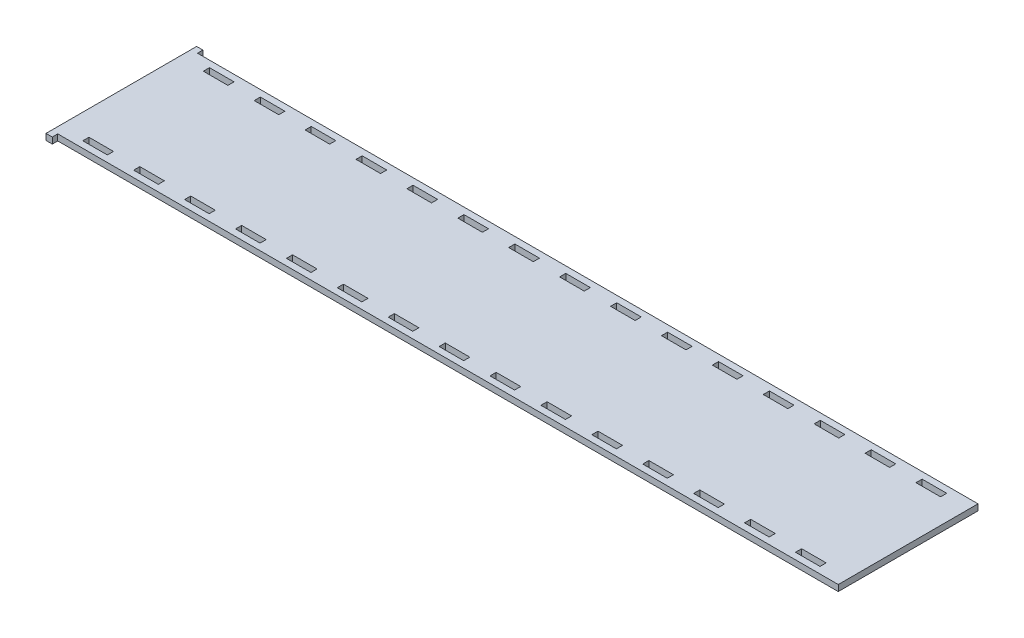
SolidWorks part; units mm, degrees
ref_plane "Front" through (0, 0, 0) normal (0, 0, 1) x (1, 0, 0)
ref_plane "Top" through (0, 0, 0) normal (0, 1, 0) x (1, 0, 0)
ref_plane "Right" through (0, 0, 0) normal (1, 0, 0) x (0, 0, -1)
sketch "Sketch1" plane through (0, 0, 0) normal (0, 1, 0) x (1, 0, 0)
  line L0 (-164.2929, -32.8311) -> (-151.3929, -32.8311) construction
  line L1 (-164.2929, -29.4529) -> (-164.2929, -32.8311) construction
  line L2 (-151.3929, -29.4529) -> (-164.2929, -29.4529) construction
  line L3 (-151.3929, -32.8311) -> (-151.3929, -29.4529) construction
  line L4 (177.7, -32.8311) -> (190.6, -32.8311) construction
  line L5 (177.7, -29.4529) -> (177.7, -32.8311) construction
  line L6 (190.6, -29.4529) -> (177.7, -29.4529) construction
  line L7 (190.6, -32.8311) -> (190.6, -29.4529) construction
  line L8 (-137.9857, -32.8311) -> (-125.0857, -32.8311) construction
  line L9 (-137.9857, -29.4529) -> (-137.9857, -32.8311) construction
  line L10 (-125.0857, -29.4529) -> (-137.9857, -29.4529) construction
  line L11 (-125.0857, -32.8311) -> (-125.0857, -29.4529) construction
  line L12 (-111.6786, -32.8311) -> (-98.7786, -32.8311) construction
  line L13 (-111.6786, -29.4529) -> (-111.6786, -32.8311) construction
  line L14 (-98.7786, -29.4529) -> (-111.6786, -29.4529) construction
  line L15 (-98.7786, -32.8311) -> (-98.7786, -29.4529) construction
  line L16 (151.3929, -32.8311) -> (164.2929, -32.8311) construction
  line L17 (151.3929, -29.4529) -> (151.3929, -32.8311) construction
  line L18 (164.2929, -29.4529) -> (151.3929, -29.4529) construction
  line L19 (164.2929, -32.8311) -> (164.2929, -29.4529) construction
  line L20 (125.0857, -32.8311) -> (137.9857, -32.8311) construction
  line L21 (125.0857, -29.4529) -> (125.0857, -32.8311) construction
  line L22 (137.9857, -29.4529) -> (125.0857, -29.4529) construction
  line L23 (137.9857, -32.8311) -> (137.9857, -29.4529) construction
  line L24 (98.7786, -32.8311) -> (111.6786, -32.8311) construction
  line L25 (98.7786, -29.4529) -> (98.7786, -32.8311) construction
  line L26 (111.6786, -29.4529) -> (98.7786, -29.4529) construction
  line L27 (111.6786, -32.8311) -> (111.6786, -29.4529) construction
  line L28 (72.4714, -32.8311) -> (85.3714, -32.8311) construction
  line L29 (72.4714, -29.4529) -> (72.4714, -32.8311) construction
  line L30 (85.3714, -29.4529) -> (72.4714, -29.4529) construction
  line L31 (85.3714, -32.8311) -> (85.3714, -29.4529) construction
  line L32 (46.1643, -32.8311) -> (59.0643, -32.8311) construction
  line L33 (46.1643, -29.4529) -> (46.1643, -32.8311) construction
  line L34 (59.0643, -29.4529) -> (46.1643, -29.4529) construction
  line L35 (59.0643, -32.8311) -> (59.0643, -29.4529) construction
  line L36 (19.8571, -32.8311) -> (32.7571, -32.8311) construction
  line L37 (19.8571, -29.4529) -> (19.8571, -32.8311) construction
  line L38 (32.7571, -29.4529) -> (19.8571, -29.4529) construction
  line L39 (32.7571, -32.8311) -> (32.7571, -29.4529) construction
  line L40 (-6.45, -32.8311) -> (6.45, -32.8311) construction
  line L41 (-6.45, -29.4529) -> (-6.45, -32.8311) construction
  line L42 (6.45, -29.4529) -> (-6.45, -29.4529) construction
  line L43 (6.45, -32.8311) -> (6.45, -29.4529) construction
  line L44 (-32.7571, -32.8311) -> (-19.8571, -32.8311) construction
  line L45 (-32.7571, -29.4529) -> (-32.7571, -32.8311) construction
  line L46 (-19.8571, -29.4529) -> (-32.7571, -29.4529) construction
  line L47 (-19.8571, -32.8311) -> (-19.8571, -29.4529) construction
  line L48 (-59.0643, -32.8311) -> (-46.1643, -32.8311) construction
  line L49 (-59.0643, -29.4529) -> (-59.0643, -32.8311) construction
  line L50 (-46.1643, -29.4529) -> (-59.0643, -29.4529) construction
  line L51 (-46.1643, -32.8311) -> (-46.1643, -29.4529) construction
  line L52 (-85.3714, -32.8311) -> (-72.4714, -32.8311) construction
  line L53 (-85.3714, -29.4529) -> (-85.3714, -32.8311) construction
  line L54 (-72.4714, -29.4529) -> (-85.3714, -29.4529) construction
  line L55 (-72.4714, -32.8311) -> (-72.4714, -29.4529) construction
  line L56 (-190.6, -32.8311) -> (-177.7, -32.8311) construction
  line L57 (-190.6, -29.4529) -> (-190.6, -32.8311) construction
  line L58 (-177.7, -29.4529) -> (-190.6, -29.4529) construction
  line L59 (-177.7, -32.8311) -> (-177.7, -29.4529) construction
  line L60 (190.6, 32.8311) -> (177.7, 32.8311) construction
  line L61 (190.6, 29.4529) -> (190.6, 32.8311) construction
  line L62 (177.7, 29.4529) -> (190.6, 29.4529) construction
  line L63 (177.7, 32.8311) -> (177.7, 29.4529) construction
  line L64 (-151.3929, 32.8311) -> (-164.2929, 32.8311) construction
  line L65 (-151.3929, 29.4529) -> (-151.3929, 32.8311) construction
  line L66 (-164.2929, 29.4529) -> (-151.3929, 29.4529) construction
  line L67 (-164.2929, 32.8311) -> (-164.2929, 29.4529) construction
  line L68 (-125.0857, 32.8311) -> (-137.9857, 32.8311) construction
  line L69 (-125.0857, 29.4529) -> (-125.0857, 32.8311) construction
  line L70 (-137.9857, 29.4529) -> (-125.0857, 29.4529) construction
  line L71 (-137.9857, 32.8311) -> (-137.9857, 29.4529) construction
  line L72 (-98.7786, 32.8311) -> (-111.6786, 32.8311) construction
  line L73 (-98.7786, 29.4529) -> (-98.7786, 32.8311) construction
  line L74 (-111.6786, 29.4529) -> (-98.7786, 29.4529) construction
  line L75 (-111.6786, 32.8311) -> (-111.6786, 29.4529) construction
  line L76 (-72.4714, 32.8311) -> (-85.3714, 32.8311) construction
  line L77 (-72.4714, 29.4529) -> (-72.4714, 32.8311) construction
  line L78 (-85.3714, 29.4529) -> (-72.4714, 29.4529) construction
  line L79 (-85.3714, 32.8311) -> (-85.3714, 29.4529) construction
  line L80 (-46.1643, 32.8311) -> (-59.0643, 32.8311) construction
  line L81 (-46.1643, 29.4529) -> (-46.1643, 32.8311) construction
  line L82 (-59.0643, 29.4529) -> (-46.1643, 29.4529) construction
  line L83 (-59.0643, 32.8311) -> (-59.0643, 29.4529) construction
  line L84 (-19.8571, 32.8311) -> (-32.7571, 32.8311) construction
  line L85 (-19.8571, 29.4529) -> (-19.8571, 32.8311) construction
  line L86 (-32.7571, 29.4529) -> (-19.8571, 29.4529) construction
  line L87 (-32.7571, 32.8311) -> (-32.7571, 29.4529) construction
  line L88 (6.45, 32.8311) -> (-6.45, 32.8311) construction
  line L89 (6.45, 29.4529) -> (6.45, 32.8311) construction
  line L90 (-6.45, 29.4529) -> (6.45, 29.4529) construction
  line L91 (-6.45, 32.8311) -> (-6.45, 29.4529) construction
  line L92 (32.7571, 32.8311) -> (19.8571, 32.8311) construction
  line L93 (32.7571, 29.4529) -> (32.7571, 32.8311) construction
  line L94 (19.8571, 29.4529) -> (32.7571, 29.4529) construction
  line L95 (19.8571, 32.8311) -> (19.8571, 29.4529) construction
  line L96 (59.0643, 32.8311) -> (46.1643, 32.8311) construction
  line L97 (59.0643, 29.4529) -> (59.0643, 32.8311) construction
  line L98 (46.1643, 29.4529) -> (59.0643, 29.4529) construction
  line L99 (46.1643, 32.8311) -> (46.1643, 29.4529) construction
  line L100 (85.3714, 32.8311) -> (72.4714, 32.8311) construction
  line L101 (85.3714, 29.4529) -> (85.3714, 32.8311) construction
  line L102 (72.4714, 29.4529) -> (85.3714, 29.4529) construction
  line L103 (72.4714, 32.8311) -> (72.4714, 29.4529) construction
  line L104 (111.6786, 32.8311) -> (98.7786, 32.8311) construction
  line L105 (111.6786, 29.4529) -> (111.6786, 32.8311) construction
  line L106 (98.7786, 29.4529) -> (111.6786, 29.4529) construction
  line L107 (98.7786, 32.8311) -> (98.7786, 29.4529) construction
  line L108 (137.9857, 32.8311) -> (125.0857, 32.8311) construction
  line L109 (137.9857, 29.4529) -> (137.9857, 32.8311) construction
  line L110 (125.0857, 29.4529) -> (137.9857, 29.4529) construction
  line L111 (125.0857, 32.8311) -> (125.0857, 29.4529) construction
  line L112 (164.2929, 32.8311) -> (151.3929, 32.8311) construction
  line L113 (164.2929, 29.4529) -> (164.2929, 32.8311) construction
  line L114 (151.3929, 29.4529) -> (164.2929, 29.4529) construction
  line L115 (151.3929, 32.8311) -> (151.3929, 29.4529) construction
  line L116 (-177.7, 32.8311) -> (-190.6, 32.8311) construction
  line L117 (-177.7, 29.4529) -> (-177.7, 32.8311) construction
  line L118 (-190.6, 29.4529) -> (-177.7, 29.4529) construction
  line L119 (-190.6, 32.8311) -> (-190.6, 29.4529) construction
  line L120 (-200.1504, 36.0061) -> (-200.1504, 38.8239) construction
  line L121 (-200.1504, 38.8239) -> (-203.2, 38.8239) construction
  line L122 (-203.2, 38.8239) -> (-203.2, -38.8239) construction
  line L123 (-203.2, -38.8239) -> (-200.1504, -38.8239) construction
  line L124 (-200.1504, -38.8239) -> (-200.1504, -36.0061) construction
  line L125 (-200.1504, -36.0061) -> (203.2, -36.0061) construction
  line L126 (203.2, -36.0061) -> (203.2, 36.0061) construction
  line L127 (203.2, 36.0061) -> (-200.1504, 36.0061) construction
  line L128 (-164.1913, -32.7295) -> (-151.4945, -32.7295)
  line L129 (-151.4945, -32.7295) -> (-151.4945, -29.5545)
  line L130 (-151.4945, -29.5545) -> (-164.1913, -29.5545)
  line L131 (-164.1913, -29.5545) -> (-164.1913, -32.7295)
  line L132 (177.8016, -32.7295) -> (190.4984, -32.7295)
  line L133 (190.4984, -32.7295) -> (190.4984, -29.5545)
  line L134 (190.4984, -29.5545) -> (177.8016, -29.5545)
  line L135 (177.8016, -29.5545) -> (177.8016, -32.7295)
  line L136 (-137.8841, -32.7295) -> (-125.1873, -32.7295)
  line L137 (-125.1873, -32.7295) -> (-125.1873, -29.5545)
  line L138 (-125.1873, -29.5545) -> (-137.8841, -29.5545)
  line L139 (-137.8841, -29.5545) -> (-137.8841, -32.7295)
  line L140 (-111.577, -32.7295) -> (-98.8802, -32.7295)
  line L141 (-98.8802, -32.7295) -> (-98.8802, -29.5545)
  line L142 (-98.8802, -29.5545) -> (-111.577, -29.5545)
  line L143 (-111.577, -29.5545) -> (-111.577, -32.7295)
  line L144 (151.4945, -32.7295) -> (164.1913, -32.7295)
  line L145 (164.1913, -32.7295) -> (164.1913, -29.5545)
  line L146 (164.1913, -29.5545) -> (151.4945, -29.5545)
  line L147 (151.4945, -29.5545) -> (151.4945, -32.7295)
  line L148 (125.1873, -32.7295) -> (137.8841, -32.7295)
  line L149 (137.8841, -32.7295) -> (137.8841, -29.5545)
  line L150 (137.8841, -29.5545) -> (125.1873, -29.5545)
  line L151 (125.1873, -29.5545) -> (125.1873, -32.7295)
  line L152 (98.8802, -32.7295) -> (111.577, -32.7295)
  line L153 (111.577, -32.7295) -> (111.577, -29.5545)
  line L154 (111.577, -29.5545) -> (98.8802, -29.5545)
  line L155 (98.8802, -29.5545) -> (98.8802, -32.7295)
  line L156 (72.573, -32.7295) -> (85.2698, -32.7295)
  line L157 (85.2698, -32.7295) -> (85.2698, -29.5545)
  line L158 (85.2698, -29.5545) -> (72.573, -29.5545)
  line L159 (72.573, -29.5545) -> (72.573, -32.7295)
  line L160 (46.2659, -32.7295) -> (58.9627, -32.7295)
  line L161 (58.9627, -32.7295) -> (58.9627, -29.5545)
  line L162 (58.9627, -29.5545) -> (46.2659, -29.5545)
  line L163 (46.2659, -29.5545) -> (46.2659, -32.7295)
  line L164 (19.9587, -32.7295) -> (32.6555, -32.7295)
  line L165 (32.6555, -32.7295) -> (32.6555, -29.5545)
  line L166 (32.6555, -29.5545) -> (19.9587, -29.5545)
  line L167 (19.9587, -29.5545) -> (19.9587, -32.7295)
  line L168 (-6.3484, -32.7295) -> (6.3484, -32.7295)
  line L169 (6.3484, -32.7295) -> (6.3484, -29.5545)
  line L170 (6.3484, -29.5545) -> (-6.3484, -29.5545)
  line L171 (-6.3484, -29.5545) -> (-6.3484, -32.7295)
  line L172 (-32.6555, -32.7295) -> (-19.9587, -32.7295)
  line L173 (-19.9587, -32.7295) -> (-19.9587, -29.5545)
  line L174 (-19.9587, -29.5545) -> (-32.6555, -29.5545)
  line L175 (-32.6555, -29.5545) -> (-32.6555, -32.7295)
  line L176 (-58.9627, -32.7295) -> (-46.2659, -32.7295)
  line L177 (-46.2659, -32.7295) -> (-46.2659, -29.5545)
  line L178 (-46.2659, -29.5545) -> (-58.9627, -29.5545)
  line L179 (-58.9627, -29.5545) -> (-58.9627, -32.7295)
  line L180 (-85.2698, -32.7295) -> (-72.573, -32.7295)
  line L181 (-72.573, -32.7295) -> (-72.573, -29.5545)
  line L182 (-72.573, -29.5545) -> (-85.2698, -29.5545)
  line L183 (-85.2698, -29.5545) -> (-85.2698, -32.7295)
  line L184 (-190.4984, -32.7295) -> (-177.8016, -32.7295)
  line L185 (-177.8016, -32.7295) -> (-177.8016, -29.5545)
  line L186 (-177.8016, -29.5545) -> (-190.4984, -29.5545)
  line L187 (-190.4984, -29.5545) -> (-190.4984, -32.7295)
  line L188 (190.4984, 32.7295) -> (177.8016, 32.7295)
  line L189 (177.8016, 32.7295) -> (177.8016, 29.5545)
  line L190 (177.8016, 29.5545) -> (190.4984, 29.5545)
  line L191 (190.4984, 29.5545) -> (190.4984, 32.7295)
  line L192 (-151.4945, 32.7295) -> (-164.1913, 32.7295)
  line L193 (-164.1913, 32.7295) -> (-164.1913, 29.5545)
  line L194 (-164.1913, 29.5545) -> (-151.4945, 29.5545)
  line L195 (-151.4945, 29.5545) -> (-151.4945, 32.7295)
  line L196 (-125.1873, 32.7295) -> (-137.8841, 32.7295)
  line L197 (-137.8841, 32.7295) -> (-137.8841, 29.5545)
  line L198 (-137.8841, 29.5545) -> (-125.1873, 29.5545)
  line L199 (-125.1873, 29.5545) -> (-125.1873, 32.7295)
  line L200 (-98.8802, 32.7295) -> (-111.577, 32.7295)
  line L201 (-111.577, 32.7295) -> (-111.577, 29.5545)
  line L202 (-111.577, 29.5545) -> (-98.8802, 29.5545)
  line L203 (-98.8802, 29.5545) -> (-98.8802, 32.7295)
  line L204 (-72.573, 32.7295) -> (-85.2698, 32.7295)
  line L205 (-85.2698, 32.7295) -> (-85.2698, 29.5545)
  line L206 (-85.2698, 29.5545) -> (-72.573, 29.5545)
  line L207 (-72.573, 29.5545) -> (-72.573, 32.7295)
  line L208 (-46.2659, 32.7295) -> (-58.9627, 32.7295)
  line L209 (-58.9627, 32.7295) -> (-58.9627, 29.5545)
  line L210 (-58.9627, 29.5545) -> (-46.2659, 29.5545)
  line L211 (-46.2659, 29.5545) -> (-46.2659, 32.7295)
  line L212 (-19.9587, 32.7295) -> (-32.6555, 32.7295)
  line L213 (-32.6555, 32.7295) -> (-32.6555, 29.5545)
  line L214 (-32.6555, 29.5545) -> (-19.9587, 29.5545)
  line L215 (-19.9587, 29.5545) -> (-19.9587, 32.7295)
  line L216 (6.3484, 32.7295) -> (-6.3484, 32.7295)
  line L217 (-6.3484, 32.7295) -> (-6.3484, 29.5545)
  line L218 (-6.3484, 29.5545) -> (6.3484, 29.5545)
  line L219 (6.3484, 29.5545) -> (6.3484, 32.7295)
  line L220 (32.6555, 32.7295) -> (19.9587, 32.7295)
  line L221 (19.9587, 32.7295) -> (19.9587, 29.5545)
  line L222 (19.9587, 29.5545) -> (32.6555, 29.5545)
  line L223 (32.6555, 29.5545) -> (32.6555, 32.7295)
  line L224 (58.9627, 32.7295) -> (46.2659, 32.7295)
  line L225 (46.2659, 32.7295) -> (46.2659, 29.5545)
  line L226 (46.2659, 29.5545) -> (58.9627, 29.5545)
  line L227 (58.9627, 29.5545) -> (58.9627, 32.7295)
  line L228 (85.2698, 32.7295) -> (72.573, 32.7295)
  line L229 (72.573, 32.7295) -> (72.573, 29.5545)
  line L230 (72.573, 29.5545) -> (85.2698, 29.5545)
  line L231 (85.2698, 29.5545) -> (85.2698, 32.7295)
  line L232 (111.577, 32.7295) -> (98.8802, 32.7295)
  line L233 (98.8802, 32.7295) -> (98.8802, 29.5545)
  line L234 (98.8802, 29.5545) -> (111.577, 29.5545)
  line L235 (111.577, 29.5545) -> (111.577, 32.7295)
  line L236 (137.8841, 32.7295) -> (125.1873, 32.7295)
  line L237 (125.1873, 32.7295) -> (125.1873, 29.5545)
  line L238 (125.1873, 29.5545) -> (137.8841, 29.5545)
  line L239 (137.8841, 29.5545) -> (137.8841, 32.7295)
  line L240 (164.1913, 32.7295) -> (151.4945, 32.7295)
  line L241 (151.4945, 32.7295) -> (151.4945, 29.5545)
  line L242 (151.4945, 29.5545) -> (164.1913, 29.5545)
  line L243 (164.1913, 29.5545) -> (164.1913, 32.7295)
  line L244 (-177.8016, 32.7295) -> (-190.4984, 32.7295)
  line L245 (-190.4984, 32.7295) -> (-190.4984, 29.5545)
  line L246 (-190.4984, 29.5545) -> (-177.8016, 29.5545)
  line L247 (-177.8016, 29.5545) -> (-177.8016, 32.7295)
  line L248 (-200.0488, -36.1077) -> (203.3016, -36.1077)
  line L249 (203.3016, -36.1077) -> (203.3016, 36.1077)
  line L250 (203.3016, 36.1077) -> (-200.0488, 36.1077)
  line L251 (-200.0488, 36.1077) -> (-200.0488, 38.9255)
  line L252 (-200.0488, 38.9255) -> (-203.3016, 38.9255)
  line L253 (-203.3016, 38.9255) -> (-203.3016, -38.9255)
  line L254 (-203.3016, -38.9255) -> (-200.0488, -38.9255)
  line L255 (-200.0488, -38.9255) -> (-200.0488, -36.1077)
  dimension "D1" = 0.1016
  dimension "D2" = 0.1016
extrude "Boss-Extrude1" add sketch "Sketch1" along normal blind 3.175
